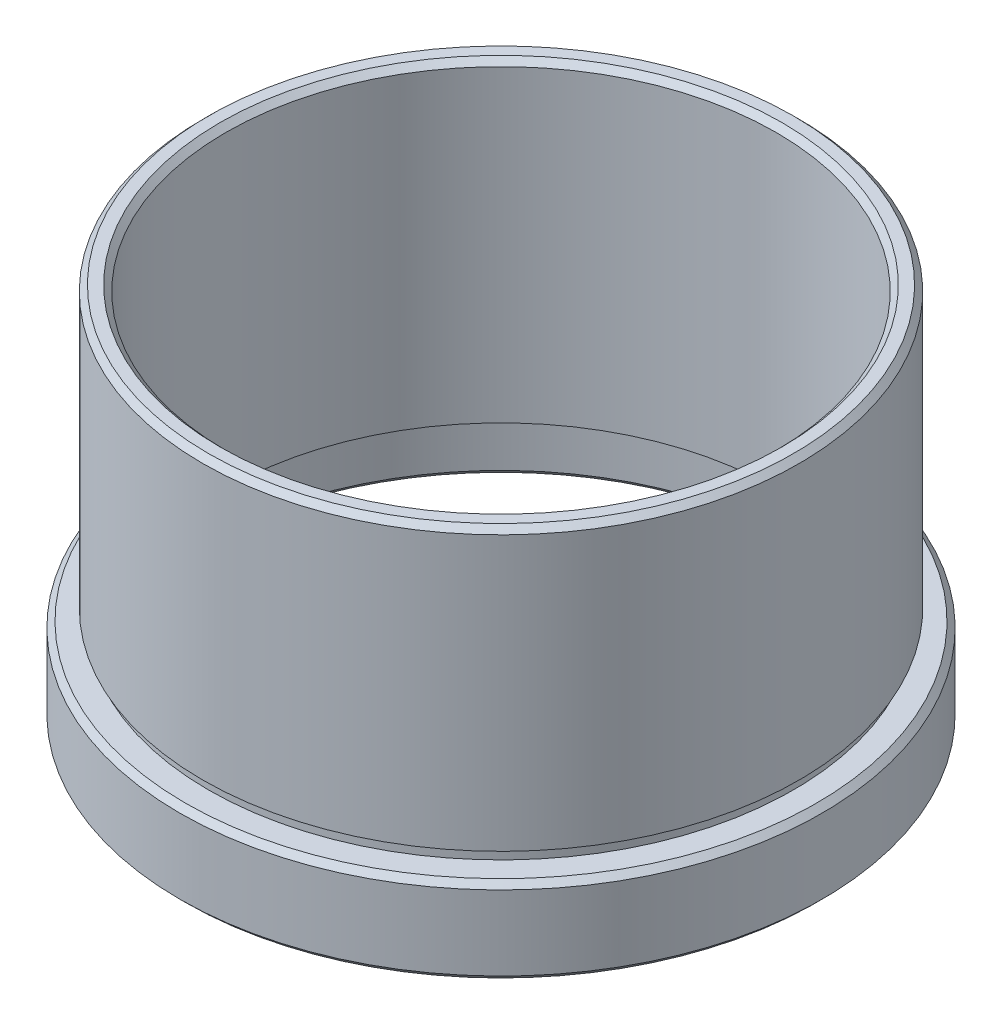
SolidWorks part; units mm, degrees
ref_plane "前视基准面" through (0, 0, 0) normal (0, 0, 1) x (1, 0, 0)
ref_plane "上视基准面" through (0, 0, 0) normal (0, 1, 0) x (1, 0, 0)
ref_plane "右视基准面" through (0, 0, 0) normal (1, 0, 0) x (0, 0, -1)
sketch "草图1" plane through (0, 0, 0) normal (0, 0, 1) x (1, 0, 0)
  line L0 (0, 44.5986) -> (0, -38.4055) construction
  line L1 (24.5, 27.0429) -> (25.5, 27.0429)
  line L2 (26, 26.5429) -> (26, 2.6429)
  line L3 (26, 2.6429) -> (25.5, 2.6429)
  line L4 (25.5, 2.6429) -> (25.5, 1.6429)
  line L5 (25.5, 1.6429) -> (27.5, 1.6429)
  line L6 (28, 1.1429) -> (28, -5.3571)
  line L7 (27.5, -5.8571) -> (26.5, -5.8571)
  line L8 (26, -5.3571) -> (26, -1.3571)
  line L9 (26, -1.3571) -> (26.1, -1.3571)
  line L10 (26.1, -1.3571) -> (26.1, -0.3571)
  line L11 (28, -5.3571) -> (27.5, -5.8571)
  line L12 (24, -0.3571) -> (24, 26.5429)
  line L13 (26.1, -0.3571) -> (24, -0.3571)
  line L14 (26.5, -5.8571) -> (26, -5.3571)
  line L15 (25.5, 27.0429) -> (26, 26.5429)
  line L16 (24, 26.5429) -> (24.5, 27.0429)
  line L17 (27.5, 1.6429) -> (28, 1.1429)
  point P3 (24, 27.0429)
  point P4 (26, 27.0429)
  point P9 (28, -5.8571)
  point P10 (28, 1.6429)
  point P11 (26, -5.8571)
  point P13 (25.5, 2.1429)
  point P14 (26.1, -0.8571)
  dimension "D2" = 28
  dimension "D3" = 26
  dimension "D4" = 26
  dimension "D5" = 24
  dimension "D6" = 7.5
  dimension "D7" = 5.5
  dimension "D8" = 1
  dimension "D9" = 1
  dimension "D10" = 25.5
  dimension "D11" = 26.1
revolve "旋转1" add sketch "草图1" angle 360 about L0
